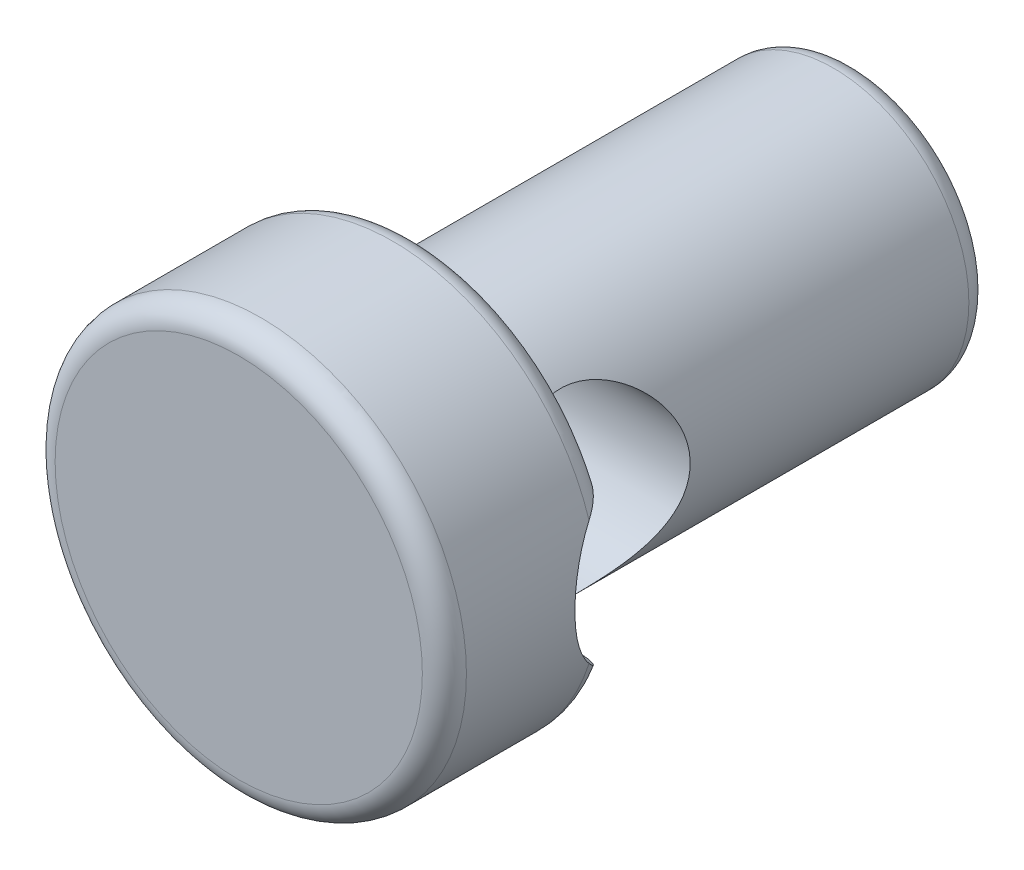
SolidWorks part; units mm, degrees
ref_plane "Front Plane" through (0, 0, 0) normal (0, 0, 1) x (1, 0, 0)
ref_plane "Top Plane" through (0, 0, 0) normal (0, 1, 0) x (1, 0, 0)
ref_plane "Right Plane" through (0, 0, 0) normal (1, 0, 0) x (0, 0, -1)
sketch "Sketch1" plane through (0, 0, 0) normal (0, 0, 1) x (1, 0, 0)
  circle A0 centre (0, 0) radius 24.5683
extrude "Extrude1" add sketch "Sketch1" along normal blind 80
sketch "Sketch2" plane through (0, 0, 80) normal (0, 0, 1) x (1, 0, 0)
  circle A0 centre (0, 0) radius 37.3396
extrude "Extrude2" add sketch "Sketch2" along normal blind 32
fillet "Fillet1" radius 4 4 edges at (24.5683, 0, 0) (24.5683, 0, 80) (37.3396, 0, 80) (37.3396, 0, 112)
ref_plane "Plane1" through (25, 0, 0) normal (1, 0, 0) x (0, 0, -1)
sketch "Sketch3" plane through (25, 0, 0) normal (1, 0, 0) x (0, 0, -1)
  line L0 (-117.9144, 0) -> (6.2895, 0) construction
  circle A0 centre (-71.45, 0) radius 16.8554
extrude "Cut-Extrude1" cut sketch "Sketch3" against normal blind 77 and the other way blind 32
